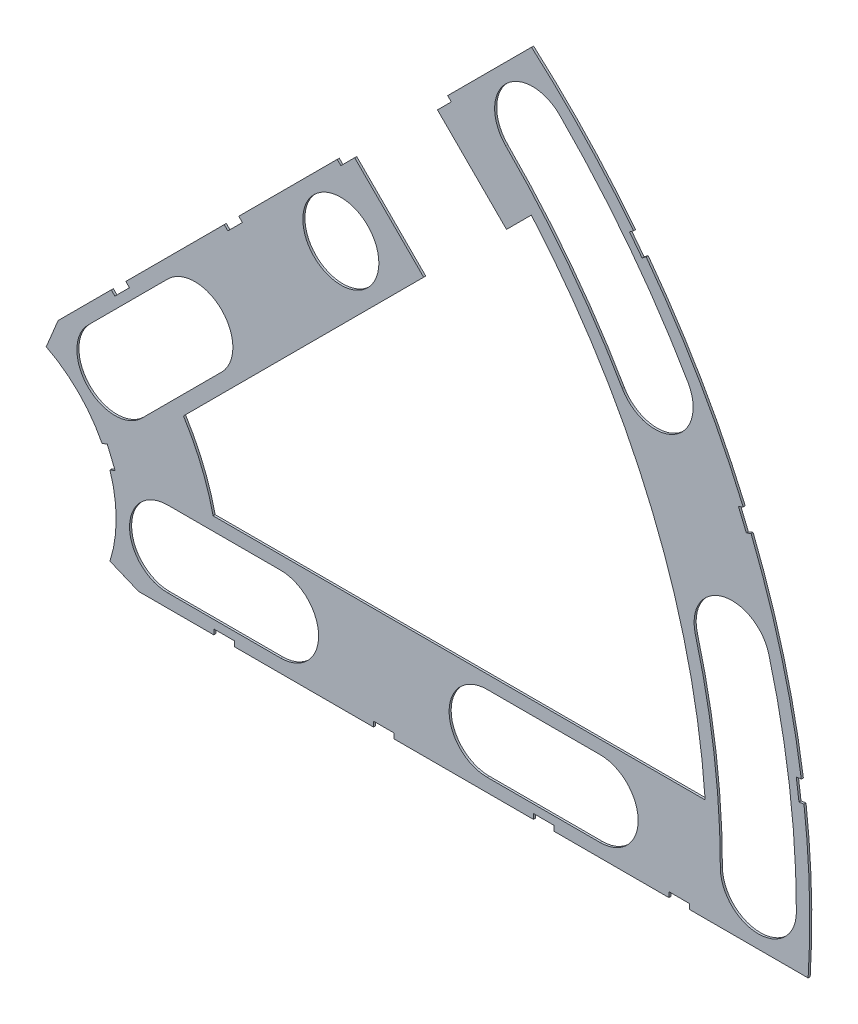
SolidWorks part; units mm, degrees
material "PTFE (general)"
ref_plane "Front Plane" through (0, 0, 0) normal (0, 0, 1) x (1, 0, 0)
ref_plane "Top Plane" through (0, 0, 0) normal (0, 1, 0) x (1, 0, 0)
ref_plane "Right Plane" through (0, 0, 0) normal (1, 0, 0) x (0, 0, -1)
sketch "Sketch1" plane through (0, 0, 0) normal (0, 0, 1) x (1, 0, 0)
  line L0 (0, 0) -> (320.3893, 0) construction
  line L1 (0, 0) -> (155.5285, 155.5285) construction
  line L2 (67.2115, 76.1917) -> (8.6967, 17.6769)
  line L3 (8.6967, 17.6769) -> (7.229, 14.1336)
  line L4 (101.4014, -6.35) -> (18.6489, -6.35)
  line L5 (15.1056, -4.8823) -> (18.6489, -6.35)
  line L6 (88.6729, 6.35) -> (27.8605, 6.35)
  line L9 (67.1914, 58.2111) -> (24.1905, 15.2102)
  line L10 (0, 0) -> (40.4486, 97.6516) construction
  line L11 (0, 0) -> (123.4567, -51.1374) construction
  line L18 (8.6967, 17.6769) -> (13.294, 8.6183) construction
  line L19 (18.6489, -6.35) -> (15.4943, 3.3063) construction
  line L20 (27.8605, 6.35) -> (27.7442, 6.7059) construction
  line L21 (24.1905, 15.2102) -> (24.3599, 14.8764) construction
  arc A0 (7.229, 14.1336) -> (15.1056, -4.8823) centre (0, 0) cw
  arc A1 (67.2115, 76.1917) -> (101.4014, -6.35) centre (0, 0) cw
  arc A2 (24.1905, 15.2102) -> (27.8605, 6.35) centre (0, 0) cw
  arc A3 (67.1914, 58.2111) -> (88.6729, 6.35) centre (0, 0) cw
  arc A8 (13.294, 8.6183) -> (15.4943, 3.3063) centre (0, 0) cw construction
  arc A9 (24.3599, 14.8764) -> (27.7442, 6.7059) centre (0, 0) cw construction
  dimension "D1" = 45
  dimension "D3" = 6.35
  dimension "D4" = 15.875
  dimension "D7" = 22.5
  dimension "D8" = 101.6
  dimension "D11" = 12.7
  dimension "D12" = 12.7
  dimension "D2" = 6.35
  dimension "D5" = 67.5
  dimension "D9" = 1.27
  dimension "D10" = 1.27
  dimension "D6" = 12.7
extrude "Boss-Extrude1" add sketch "Sketch1" along normal blind 0.254
sketch "Sketch2" plane through (0, 0, 0.254) normal (0, 0, 1) x (1, 0, 0)
  line L0 (0, 0) -> (101.6, 0) construction
  line L1 (0, 0) -> (71.842, 71.842) construction
  line L3 (0, 0) -> (22.225, 0) construction
  line L4 (0, 0) -> (15.7154, 15.7154) construction
  line L5 (0, 0) -> (95.25, 0) construction
  line L6 (0, 0) -> (92.0044, 24.6525) construction
  arc A0 (101.4014, -6.35) -> (67.2115, 76.1917) centre (0, 0) ccw construction
  circle A1 centre (22.225, 0) radius 4.699
  arc A2 (15.1056, -4.8823) -> (7.229, 14.1336) centre (0, 0) ccw construction
  circle A3 centre (36.195, 0) radius 4.699
  circle A4 centre (61.722, 0) radius 4.699
  circle A5 centre (75.692, 0) radius 4.699
  circle A6 centre (95.25, 0) radius 4.699
  circle A7 centre (15.7154, 15.7154) radius 4.699
  circle A8 centre (25.5937, 25.5937) radius 4.699
  circle A9 centre (43.644, 43.644) radius 4.699
  circle A10 centre (53.5223, 53.5223) radius 4.699
  circle A11 centre (92.0044, 24.6525) radius 4.699
  circle A12 centre (82.4889, 47.625) radius 4.699
  circle A13 centre (67.3519, 67.3519) radius 4.699
  dimension "D3" = 9.398
  dimension "D1" = 45
  dimension "D2" = 6.35
  dimension "D4" = 6.35
  dimension "D5" = 13.97
  dimension "D7" = 13.97
  dimension "D8" = 19.558
  dimension "D9" = 45
  dimension "D10" = 15
  dimension "D11" = 25.527
  dimension "D6" = 2
extrude "Cut-Extrude1" cut sketch "Sketch2" against normal through all
sketch "Sketch3" plane through (0, 0, 0.254) normal (0, 0, 1) x (1, 0, 0)
  line L0 (15.2664, 24.2467) -> (17.0625, 26.0427)
  line L1 (15.2664, 24.2467) -> (15.7154, 23.7977)
  line L2 (17.0625, 26.0427) -> (17.5115, 25.5937)
  line L3 (15.7154, 23.7977) -> (17.5115, 25.5937)
  line L4 (67.2115, 76.1917) -> (8.6967, 17.6769) construction
  line L5 (44.9911, 53.9713) -> (43.195, 52.1753)
  line L6 (44.9911, 53.9713) -> (45.4401, 53.5223)
  line L7 (43.195, 52.1753) -> (43.644, 51.7263)
  line L8 (45.4401, 53.5223) -> (43.644, 51.7263)
  line L9 (27.94, -6.35) -> (30.48, -6.35)
  line L10 (27.94, -6.35) -> (27.94, -5.715)
  line L11 (30.48, -6.35) -> (30.48, -5.715)
  line L12 (27.94, -5.715) -> (30.48, -5.715)
  line L13 (18.6489, -6.35) -> (101.4014, -6.35) construction
  line L14 (67.437, -6.35) -> (69.977, -6.35)
  line L15 (67.437, -6.35) -> (67.437, -5.715)
  line L16 (69.977, -6.35) -> (69.977, -5.715)
  line L17 (67.437, -5.715) -> (69.977, -5.715)
  line L18 (29.2307, 38.211) -> (31.0268, 40.007)
  line L19 (29.2307, 38.211) -> (29.6797, 37.762)
  line L20 (31.0268, 40.007) -> (31.4758, 39.558)
  line L21 (29.6797, 37.762) -> (31.4758, 39.558)
  line L22 (56.845, 65.8253) -> (55.049, 64.0292)
  line L23 (56.845, 65.8253) -> (57.294, 65.3763)
  line L24 (55.049, 64.0292) -> (55.498, 63.5802)
  line L25 (57.294, 65.3763) -> (55.498, 63.5802)
  line L26 (47.6885, -6.35) -> (50.2285, -6.35)
  line L27 (47.6885, -6.35) -> (47.6885, -5.715)
  line L28 (50.2285, -6.35) -> (50.2285, -5.715)
  line L29 (47.6885, -5.715) -> (50.2285, -5.715)
  line L30 (84.201, -6.35) -> (86.741, -6.35)
  line L31 (84.201, -6.35) -> (84.201, -5.715)
  line L32 (86.741, -6.35) -> (86.741, -5.715)
  line L33 (84.201, -5.715) -> (86.741, -5.715)
  line L34 (0, 0) -> (100.7308, 13.2615) construction
  line L35 (0, 0) -> (93.8662, 38.8806) construction
  line L36 (0, 0) -> (80.6047, 61.8502) construction
  line L37 (0, 0) -> (101.6, 0) construction
  line L38 (99.9355, 14.4377) -> (100.267, 11.9194)
  line L39 (99.9355, 14.4377) -> (101.1946, 14.6035)
  line L40 (100.267, 11.9194) -> (101.5261, 12.0852)
  line L41 (101.1946, 14.6035) -> (101.5261, 12.0852)
  line L42 (99.9355, 14.4377) -> (101.5261, 12.0852) construction
  line L43 (100.267, 11.9194) -> (101.1946, 14.6035) construction
  line L44 (93.7655, 37.4643) -> (94.9388, 37.9503)
  line L45 (93.7655, 37.4643) -> (92.7935, 39.811)
  line L46 (94.9388, 37.9503) -> (93.9668, 40.297)
  line L47 (92.7935, 39.811) -> (93.9668, 40.297)
  line L48 (93.7655, 37.4643) -> (93.9668, 40.297) construction
  line L49 (94.9388, 37.9503) -> (92.7935, 39.811) construction
  line L50 (79.3278, 62.4712) -> (80.874, 60.456)
  line L51 (79.3278, 62.4712) -> (80.3354, 63.2443)
  line L52 (80.874, 60.456) -> (81.8816, 61.2292)
  line L53 (80.3354, 63.2443) -> (81.8816, 61.2292)
  line L54 (79.3278, 62.4712) -> (81.8816, 61.2292) construction
  line L55 (80.874, 60.456) -> (80.3354, 63.2443) construction
  line L56 (13.5939, 7.0054) -> (14.5659, 4.6588)
  line L57 (13.5939, 7.0054) -> (14.7672, 7.4914)
  line L58 (14.5659, 4.6588) -> (15.7393, 5.1448)
  line L59 (14.7672, 7.4914) -> (15.7393, 5.1448)
  line L60 (13.5939, 7.0054) -> (15.7393, 5.1448) construction
  line L61 (14.5659, 4.6588) -> (14.7672, 7.4914) construction
  circle A0 centre (15.7154, 15.7154) radius 4.699 construction
  circle A1 centre (43.644, 43.644) radius 4.699 construction
  circle A2 centre (22.225, 0) radius 4.699 construction
  circle A3 centre (61.722, 0) radius 4.699 construction
  arc A4 (101.4014, -6.35) -> (67.2115, 76.1917) centre (0, 0) ccw construction
  arc A9 (15.1056, -4.8823) -> (7.229, 14.1336) centre (0, 0) ccw construction
  circle A10 centre (25.5937, 25.5937) radius 4.699 construction
  circle A11 centre (53.5223, 53.5223) radius 4.699 construction
  circle A12 centre (36.195, 0) radius 4.699 construction
  circle A13 centre (75.692, 0) radius 4.699 construction
  point P75 (14.6666, 6.0751)
  dimension "D2" = 5.715
  dimension "D3" = 2.54
  dimension "D6" = 5.715
  dimension "D8" = 0.635
  dimension "D9" = 5.715
  dimension "D12" = 5.715
  dimension "D4" = 7.5
  dimension "D5" = 22.5
  dimension "D7" = 37.5
  dimension "D10" = 90
  dimension "D11" = 1.27
  dimension "D14" = 0.635
  dimension "D15" = 90
  dimension "D18" = 0.635
  dimension "D19" = 90
  dimension "D22" = 0.635
  dimension "D20" = 1.27
  dimension "D17" = 0.635
  dimension "D13" = 11.4935
  dimension "D16" = 8.509
  dimension "D21" = 11.4935
  dimension "D23" = 8.509
extrude "Cut-Extrude2" cut sketch "Sketch3" against normal through all
sketch "Sketch5" plane through (0, 0, 0.254) normal (0, 0, 1) x (1, 0, 0)
  line L0 (53.8815, 44.9013) -> (64.119, 55.1388)
  line L1 (53.8815, 44.9013) -> (44.9013, 53.8815)
  line L2 (64.119, 55.1388) -> (55.1388, 64.119)
  line L3 (57.294, 65.3763) -> (56.845, 65.8253) construction
  line L4 (44.9013, 53.8815) -> (55.1388, 64.119)
  line L5 (67.1914, 58.2111) -> (24.1905, 15.2102) construction
  line L6 (67.2115, 76.1917) -> (56.845, 65.8253) construction
  line L9 (43.195, 52.1753) -> (43.644, 51.7263) construction
  dimension "D1" = 2.413
  dimension "D2" = 2.413
sketch "Sketch6" plane through (0, 0, 0.254) normal (0, 0, 1) x (1, 0, 0)
  line L0 (0, 0) -> (101.6, 0) construction
  line L1 (0, 0) -> (71.842, 71.842) construction
  line L2 (0, 0) -> (87.9882, 50.8) construction
  line L3 (0, 0) -> (98.1381, 26.296) construction
  line L4 (15.7154, 15.7154) -> (25.5937, 25.5937) construction
  line L5 (12.3928, 19.0381) -> (22.271, 28.9164)
  line L6 (19.0381, 12.3928) -> (28.9164, 22.271)
  line L10 (22.225, 0) -> (36.195, 0) construction
  line L11 (22.225, 4.699) -> (36.195, 4.699)
  line L12 (22.225, -4.699) -> (36.195, -4.699)
  line L13 (61.722, 0) -> (75.692, 0) construction
  line L14 (61.722, 4.699) -> (75.692, 4.699)
  line L15 (61.722, -4.699) -> (75.692, -4.699)
  arc A0 (79.8253, 62.8529) -> (67.2115, 76.1917) centre (0, 0) ccw construction
  arc A1 (12.3928, 19.0381) -> (19.0381, 12.3928) centre (15.7154, 15.7154) ccw
  arc A2 (28.9164, 22.271) -> (22.271, 28.9164) centre (25.5937, 25.5937) ccw
  circle A3 centre (25.5937, 25.5937) radius 4.699 construction
  arc A5 (101.4014, -6.35) -> (100.8887, 12.0013) centre (0, 0) ccw construction
  arc A6 (22.225, 4.699) -> (22.225, -4.699) centre (22.225, 0) ccw
  arc A7 (93.3728, 40.0509) -> (81.3715, 60.8378) centre (0, 0) ccw construction
  arc A8 (100.5572, 14.5196) -> (94.3448, 37.7043) centre (0, 0) ccw construction
  arc A9 (36.195, -4.699) -> (36.195, 4.699) centre (36.195, 0) ccw
  arc A10 (61.722, 4.699) -> (61.722, -4.699) centre (61.722, 0) ccw
  arc A11 (75.692, -4.699) -> (75.692, 4.699) centre (75.692, 0) ccw
  arc A12 (95.25, 0) -> (92.0044, 24.6525) centre (0, 0) ccw construction
  arc A13 (99.949, 0) -> (96.5433, 25.8687) centre (0, 0) ccw
  arc A14 (90.551, 0) -> (87.4655, 23.4363) centre (0, 0) ccw
  arc A15 (90.551, 0) -> (99.949, 0) centre (95.25, 0) ccw
  arc A16 (96.5433, 25.8687) -> (87.4655, 23.4363) centre (92.0044, 24.6525) ccw
  arc A17 (82.4889, 47.625) -> (67.3519, 67.3519) centre (0, 0) ccw construction
  arc A18 (86.5584, 49.9745) -> (70.6746, 70.6746) centre (0, 0) ccw
  arc A19 (78.4195, 45.2755) -> (64.0292, 64.0292) centre (0, 0) ccw
  arc A20 (78.4195, 45.2755) -> (86.5584, 49.9745) centre (82.4889, 47.625) ccw
  arc A21 (70.6746, 70.6746) -> (64.0292, 64.0292) centre (67.3519, 67.3519) ccw
  point P4 (20.6546, 20.6546)
  point P37 (29.21, 0)
  point P48 (68.707, 0)
  point P61 (94.4351, 12.4326)
  point P68 (75.5669, 57.9845)
  dimension "D2" = 9.398
  dimension "D3" = 9.398
  dimension "D1" = 45
  dimension "D4" = 9.398
  dimension "D5" = 9.398
extrude "Cut-Extrude4" cut sketch "Sketch6" against normal through all
extrude "Cut-Extrude5" cut sketch "Sketch5" against normal through all
equation "\"cSep\"= 1.005"
equation "\"D11@Sketch2\"=\"cSep\""
equation "\"cSep2\"= \"D8@Sketch2\""
equation "\"D13@Sketch3\"=\"cSep\"/2-.05"
equation "\"D16@Sketch3\"=\"cSep2\"/2-.05"
equation "\"D21@Sketch3\"=\"cSep\"/2-.05"
equation "\"D23@Sketch3\"=\"cSep2\"/2-.05"
